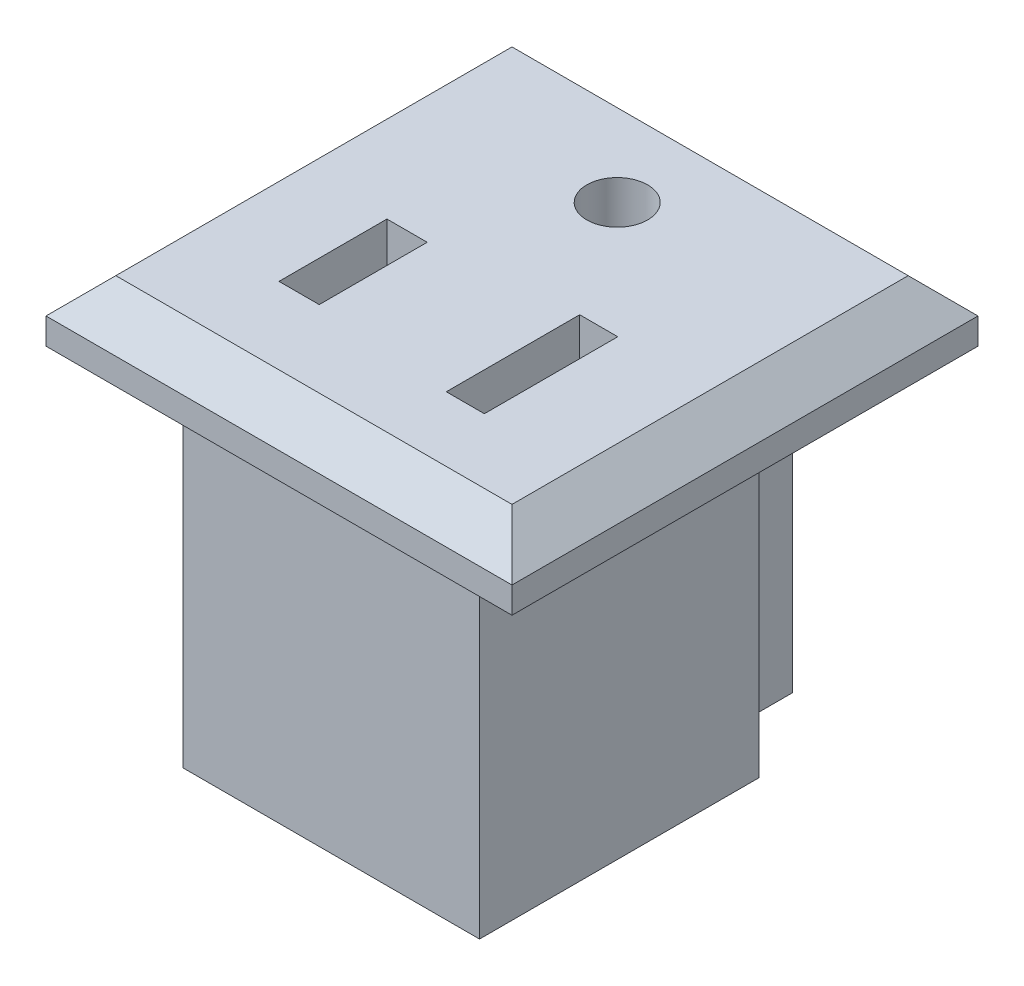
SolidWorks part; units mm, degrees
ref_plane "Front Plane" through (0, 0, 0) normal (0, 0, 1) x (1, 0, 0)
ref_plane "Top Plane" through (0, 0, 0) normal (0, 1, 0) x (1, 0, 0)
ref_plane "Right Plane" through (0, 0, 0) normal (1, 0, 0) x (0, 0, -1)
sketch "Sketch1" plane through (0, 0, 0) normal (0, 1, 0) x (1, 0, 0)
  line L1 (-17.6815, 0) -> (9.0185, 0)
  line L2 (-17.6815, 0) -> (-17.6815, 26.7)
  line L3 (-17.6815, 26.7) -> (9.0185, 26.7)
  line L4 (9.0185, 0) -> (9.0185, 26.7)
  dimension "D1" = 26.7
  dimension "D2" = 26.7
extrude "Boss-Extrude1" add sketch "Sketch1" along normal blind 3.5
chamfer "Chamfer1" distance 2 angle 45 4 edges at (-4.3315, 3.5, -26.7) (9.0185, 3.5, -13.35) (-4.3315, 3.5, 0) (-17.6815, 3.5, -13.35)
sketch "Sketch2" plane through (0, 0, 0) normal (0, -1, 0) x (1, 0, 0)
  line L0 (-17.6815, 0) -> (9.0185, 0) construction
  line L1 (-12.8415, -3) -> (4.1585, -3)
  line L2 (-12.8415, -3) -> (-12.8415, -19)
  line L3 (-12.8415, -19) -> (4.1585, -19)
  line L4 (4.1585, -3) -> (4.1585, -19)
  line L5 (9.0185, 0) -> (9.0185, -26.7) construction
  dimension "D1" = 17
  dimension "D2" = 16
  dimension "D3" = 3
  dimension "D4" = 4.86
extrude "Boss-Extrude2" add sketch "Sketch2" along normal blind 20
sketch "Sketch3" plane through (0, 0, 0) normal (0, -1, 0) x (1, 0, 0)
  line L0 (-12.8415, -19) -> (4.1585, -19) construction
  line L1 (-8.9975, -19) -> (0.9018, -19)
  line L2 (-8.9975, -19) -> (-8.9975, -24.2)
  line L3 (-8.9975, -24.2) -> (0.9018, -24.2)
  line L4 (0.9018, -19) -> (0.9018, -24.2)
  line L5 (9.0185, -26.7) -> (-17.6815, -26.7) construction
  dimension "D1" = 2.5
extrude "Boss-Extrude3" add sketch "Sketch3" along normal blind 20
sketch "Sketch4" plane through (0, 3.5, 0) normal (0, 1, 0) x (1, 0, 0)
  line L1 (1.7291, 5.7064) -> (-0.453, 5.7064)
  line L2 (1.7291, 5.7064) -> (1.7291, 13.349)
  line L3 (1.7291, 13.349) -> (-0.453, 13.349)
  line L4 (-0.453, 5.7064) -> (-0.453, 13.349)
  line L5 (-8.4173, 6.3903) -> (-10.7231, 6.3903)
  line L6 (-8.4173, 6.3903) -> (-8.4173, 12.577)
  line L7 (-8.4173, 12.577) -> (-10.7231, 12.577)
  line L8 (-10.7231, 6.3903) -> (-10.7231, 12.577)
  circle A0 centre (-4.9529, 19.9991) radius 1.7439
extrude "Cut-Extrude1" cut sketch "Sketch4" against normal blind 5
